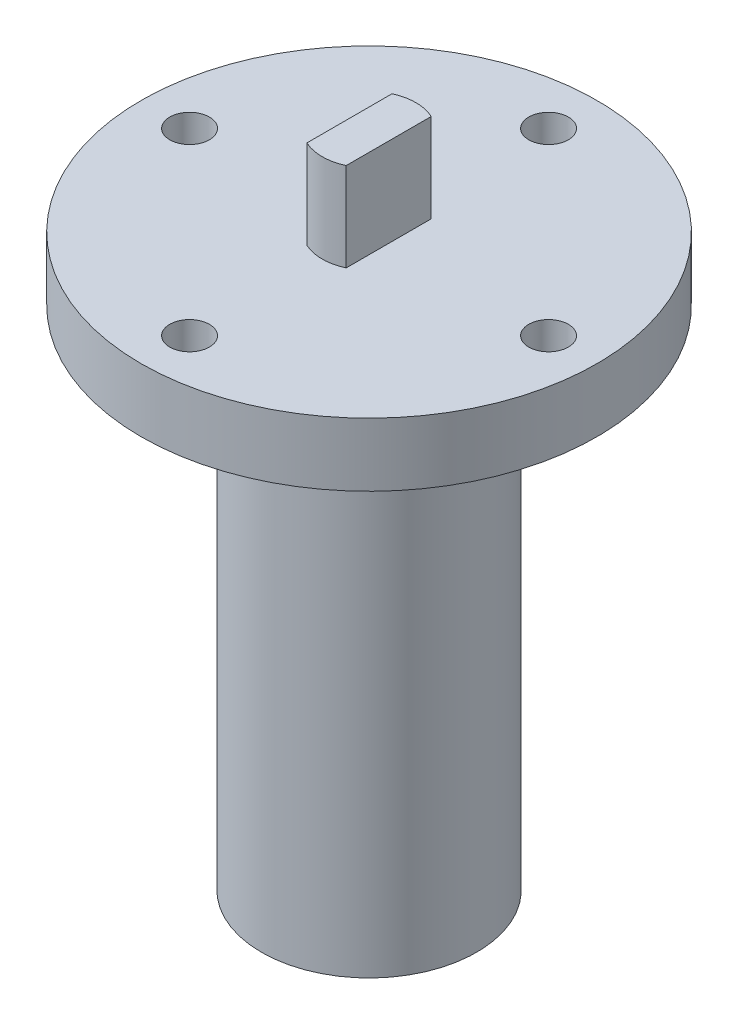
SolidWorks part; units mm, degrees
ref_plane "Front Plane" through (0, 0, 0) normal (0, 0, 1) x (1, 0, 0)
ref_plane "Top Plane" through (0, 0, 0) normal (0, 1, 0) x (1, 0, 0)
ref_plane "Right Plane" through (0, 0, 0) normal (1, 0, 0) x (0, 0, -1)
sketch "Sketch1" plane through (0, 0, 0) normal (0, 1, 0) x (1, 0, 0)
  circle A0 centre (0, 0) radius 22.86
  dimension "D1" = 45.72
extrude "Boss-Extrude1" add sketch "Sketch1" along normal blind 6.35
sketch "Sketch2" plane through (0, 6.35, 0) normal (0, 1, 0) x (1, 0, 0)
  line L0 (1.9685, 4.2668) -> (1.9685, -4.2668)
  line L1 (-1.9685, 4.2668) -> (-1.9685, -4.2668)
  line L2 (0, 0) -> (1.9685, 0) construction
  line L3 (0, 0) -> (-1.9685, 0) construction
  circle A0 centre (0, 0) radius 4.699
  point P7 (0, 0)
  point P10 (0, 0)
  point P11 (0, 0)
  dimension "D1" = 9.398
  dimension "D2" = 1.9685
  dimension "D3" = 1.9685
extrude "Boss-Extrude2" add sketch "Sketch2" along normal blind 8.89 contours L0 A0 L1
sketch "Sketch3" plane through (0, 0, 0) normal (0, -1, 0) x (1, 0, 0)
  circle A0 centre (0, 0) radius 10.795
  dimension "D1" = 21.59
extrude "Boss-Extrude3" add sketch "Sketch3" along normal blind 50.8
chamfer "Chamfer1" distance 3.81 angle 45 1 edges at (0, 0, -10.795)
sketch "Sketch4" plane through (0, 6.35, 0) normal (0, 1, 0) x (1, 0, 0)
  line L0 (0, 0) -> (0, 18) construction
  circle A0 centre (0, 0) radius 18 construction
  dimension "D1" = 36
hole_wizard "5/32 (0.15625) Diameter Hole1" positions "Sketch5" profile "Sketch6" hole size "5/32" standard "ANSI Inch" end condition up to next
sketch "Sketch5" plane through (0, 6.35, 0) normal (0, 1, 0) x (1, 0, 0)
  point P0 (0, 18)
sketch "Sketch6" plane through (0, 6.35, -18) normal (1, 0, 0) x (0, 0, 1)
  line L0 (0, 0) -> (0, 6.351)
  line L1 (0, 6.351) -> (1.9844, 6.351)
  line L2 (1.9844, 6.351) -> (1.9844, 0)
  line L5 (1.9844, 0) -> (0, 0)
  line L11 (0, -6.35) -> (0, 107.95) construction
  dimension "Thru Hole Dia." = 3.9688
  dimension "Thru Hole Depth" = 6.351
pattern_circular "CirPattern1" count 4 over 360 about axis through (0, 0, 0) along (0, 1, 0) of "5/32 (0.15625) Diameter Hole1"
equation "\"D2@Sketch2\"=(.37-.215)/2"
